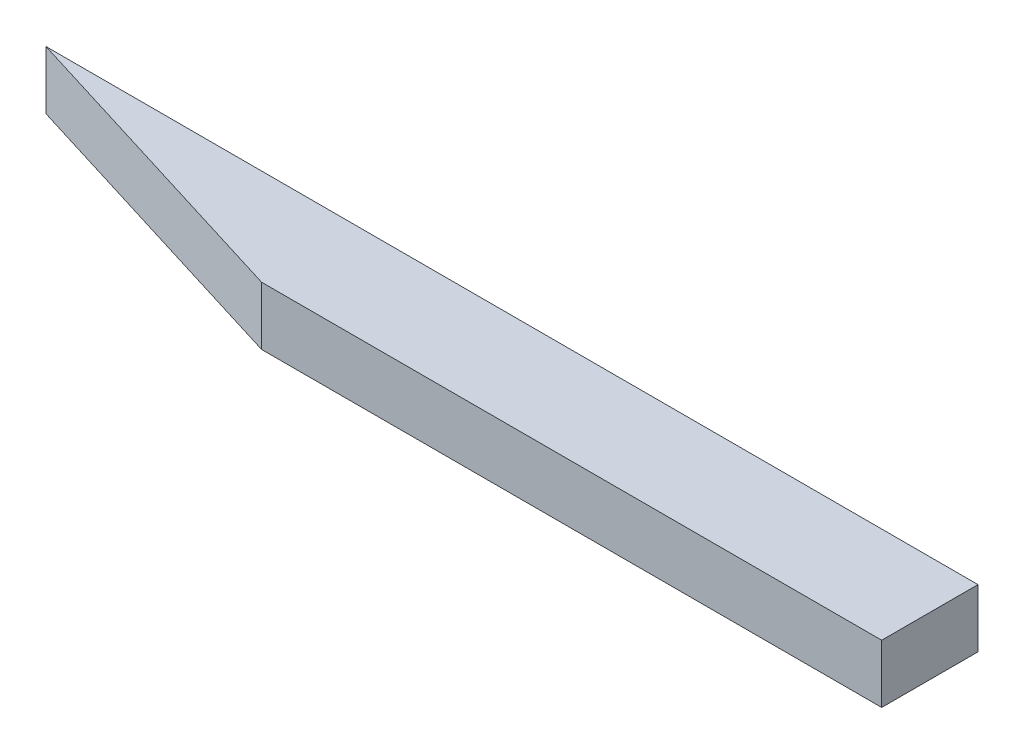
SolidWorks part; units mm, degrees
ref_plane "Front Plane" through (0, 0, 0) normal (0, 0, 1) x (1, 0, 0)
ref_plane "Top Plane" through (0, 0, 0) normal (0, 1, 0) x (1, 0, 0)
ref_plane "Right Plane" through (0, 0, 0) normal (1, 0, 0) x (0, 0, -1)
sketch "Sketch1" plane through (0, 0, 0) normal (0, 1, 0) x (1, 0, 0)
  line L0 (0, 0) -> (203.2, 0)
  line L1 (0, 0) -> (68, -21)
  line L2 (68, -21) -> (203.2, -21)
  line L3 (68, 0) -> (68, -21) construction
  line L4 (203.2, 0) -> (203.2, -21)
  line L5 (203.2, -21) -> (109.1651, -21) construction
  dimension "D1" = 68
  dimension "D2" = 21
  dimension "D3" = 0
  dimension "D4" = 203.2
extrude "Boss-Extrude1" add sketch "Sketch1" along normal mid plane 12.7
